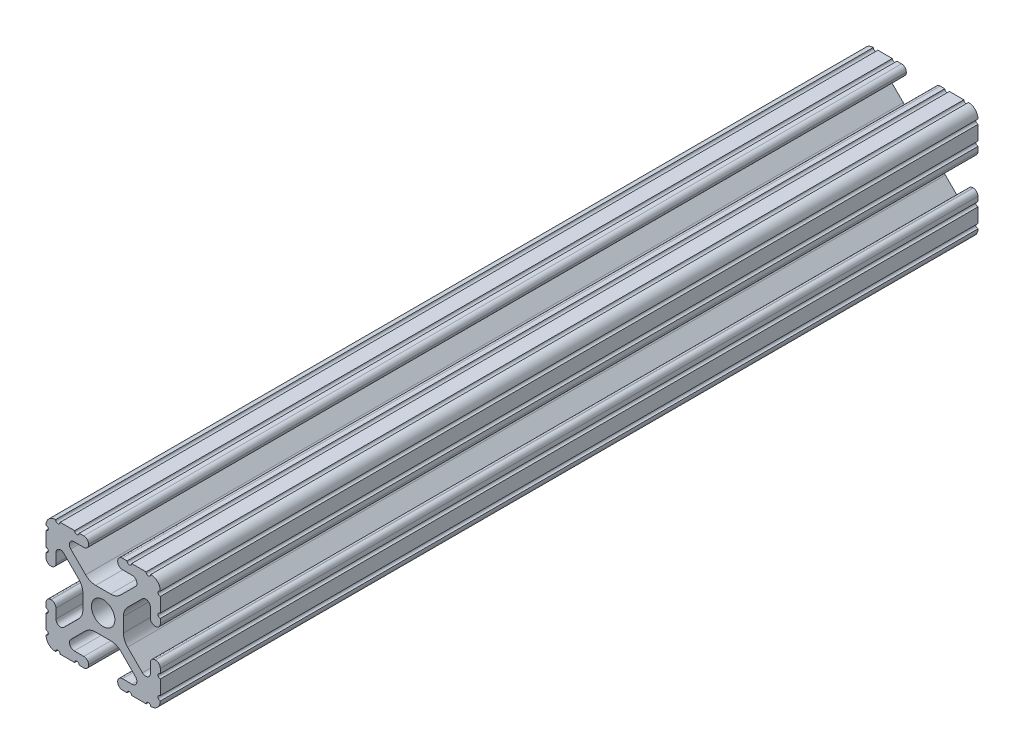
SolidWorks part; units mm, degrees
ref_plane "Front Plane" through (0, 0, 0) normal (0, 0, 1) x (1, 0, 0)
ref_plane "Top Plane" through (0, 0, 0) normal (0, 1, 0) x (1, 0, 0)
ref_plane "Right Plane" through (0, 0, 0) normal (1, 0, 0) x (0, 0, -1)
sketch "Sketch1" plane through (0, 0, 0) normal (0, 0, 1) x (1, 0, 0)
  line L88 (-7.1797, -8.6452) -> (-3.9523, -5.4237)
  line L89 (-1.7093, -4.4958) -> (1.7093, -4.4958)
  line L90 (3.9523, -5.4237) -> (7.1797, -8.6452)
  line L91 (6.4164, -10.4902) -> (4.2875, -10.4902)
  line L92 (3.2385, -11.5392) -> (3.2385, -11.651)
  line L93 (4.2875, -12.7) -> (5.3171, -12.7)
  line L94 (6.3331, -12.7) -> (9.5504, -12.7)
  line L95 (12.7, -9.5504) -> (12.7, -6.3331)
  line L96 (12.7, -5.3171) -> (12.7, -4.2875)
  line L97 (11.651, -3.2385) -> (11.5392, -3.2385)
  line L98 (10.4902, -4.2875) -> (10.4902, -6.4021)
  line L99 (8.7371, -7.1294) -> (5.441, -3.8408)
  line L100 (4.5085, -1.5932) -> (4.5085, 1.5932)
  line L101 (5.441, 3.8408) -> (8.7371, 7.1294)
  line L102 (10.4902, 6.4021) -> (10.4902, 4.2875)
  line L103 (11.5392, 3.2385) -> (11.651, 3.2385)
  line L104 (12.7, 4.2875) -> (12.7, 5.3171)
  line L105 (12.7, 6.3331) -> (12.7, 9.5504)
  line L106 (9.5504, 12.7) -> (6.3331, 12.7)
  line L107 (5.3171, 12.7) -> (4.2875, 12.7)
  line L108 (3.2385, 11.651) -> (3.2385, 11.5392)
  line L109 (4.2875, 10.4902) -> (6.4768, 10.4902)
  line L110 (7.207, 8.7244) -> (3.8983, 5.4232)
  line L111 (1.6558, 4.4958) -> (-1.6558, 4.4958)
  line L112 (-3.8983, 5.4232) -> (-7.207, 8.7244)
  line L113 (-6.4768, 10.4902) -> (-4.2875, 10.4902)
  line L114 (-3.2385, 11.5392) -> (-3.2385, 11.651)
  line L115 (-4.2875, 12.7) -> (-5.3171, 12.7)
  line L116 (-6.3331, 12.7) -> (-9.5504, 12.7)
  line L117 (-12.7, 9.5504) -> (-12.7, 6.3331)
  line L118 (-12.7, 5.3171) -> (-12.7, 4.2875)
  line L119 (-11.651, 3.2385) -> (-11.5392, 3.2385)
  line L120 (-10.4902, 4.2875) -> (-10.4902, 6.4021)
  line L121 (-8.7371, 7.1294) -> (-5.441, 3.8408)
  line L122 (-4.5085, 1.5932) -> (-4.5085, -1.5932)
  line L123 (-5.441, -3.8408) -> (-8.7371, -7.1294)
  line L124 (-10.4902, -6.4021) -> (-10.4902, -4.2875)
  line L125 (-11.5392, -3.2385) -> (-11.651, -3.2385)
  line L126 (-12.7, -4.2875) -> (-12.7, -5.3171)
  line L127 (-12.7, -6.3331) -> (-12.7, -9.5504)
  line L128 (-9.5504, -12.7) -> (-6.3331, -12.7)
  line L129 (-5.3171, -12.7) -> (-4.2875, -12.7)
  line L130 (-3.2385, -11.651) -> (-3.2385, -11.5392)
  line L131 (-4.2875, -10.4902) -> (-6.4164, -10.4902)
  circle A1 centre (0, 0) radius 2.6035
  arc A104 (-7.1797, -8.6452) -> (-6.4164, -10.4902) centre (-6.4164, -9.4098) ccw
  arc A105 (-1.7093, -4.4958) -> (-3.9523, -5.4237) centre (-1.7093, -7.6708) ccw
  arc A106 (3.9523, -5.4237) -> (1.7093, -4.4958) centre (1.7093, -7.6708) ccw
  arc A107 (6.4164, -10.4902) -> (7.1797, -8.6452) centre (6.4164, -9.4098) ccw
  arc A108 (4.2875, -10.4902) -> (3.2385, -11.5392) centre (4.2875, -11.5392) ccw
  arc A109 (3.2385, -11.651) -> (4.2875, -12.7) centre (4.2875, -11.651) ccw
  arc A110 (6.3331, -12.7) -> (5.3171, -12.7) centre (5.8251, -12.7) ccw
  arc A111 (10.5664, -12.6998) -> (9.5504, -12.7) centre (10.0584, -12.7) ccw
  arc A112 (10.5664, -12.6998) -> (12.6998, -10.5664) centre (10.5918, -10.5918) ccw
  arc A113 (12.7, -9.5504) -> (12.6998, -10.5664) centre (12.7, -10.0584) ccw
  arc A114 (12.7, -5.3171) -> (12.7, -6.3331) centre (12.7, -5.8251) ccw
  arc A115 (12.7, -4.2875) -> (11.651, -3.2385) centre (11.651, -4.2875) ccw
  arc A116 (11.5392, -3.2385) -> (10.4902, -4.2875) centre (11.5392, -4.2875) ccw
  arc A117 (8.7371, -7.1294) -> (10.4902, -6.4021) centre (9.4628, -6.4021) ccw
  arc A118 (4.5085, -1.5932) -> (5.441, -3.8408) centre (7.6835, -1.5932) ccw
  arc A119 (5.441, 3.8408) -> (4.5085, 1.5932) centre (7.6835, 1.5932) ccw
  arc A120 (10.4902, 6.4021) -> (8.7371, 7.1294) centre (9.4628, 6.4021) ccw
  arc A121 (10.4902, 4.2875) -> (11.5392, 3.2385) centre (11.5392, 4.2875) ccw
  arc A122 (11.651, 3.2385) -> (12.7, 4.2875) centre (11.651, 4.2875) ccw
  arc A123 (12.7, 6.3331) -> (12.7, 5.3171) centre (12.7, 5.8251) ccw
  arc A124 (12.6998, 10.5664) -> (12.7, 9.5504) centre (12.7, 10.0584) ccw
  arc A125 (12.6998, 10.5664) -> (10.5664, 12.6998) centre (10.5918, 10.5918) ccw
  arc A126 (9.5504, 12.7) -> (10.5664, 12.6998) centre (10.0584, 12.7) ccw
  arc A127 (5.3171, 12.7) -> (6.3331, 12.7) centre (5.8251, 12.7) ccw
  arc A128 (4.2875, 12.7) -> (3.2385, 11.651) centre (4.2875, 11.651) ccw
  arc A129 (3.2385, 11.5392) -> (4.2875, 10.4902) centre (4.2875, 11.5392) ccw
  arc A130 (7.207, 8.7244) -> (6.4768, 10.4902) centre (6.4768, 9.4563) ccw
  arc A131 (1.6558, 4.4958) -> (3.8983, 5.4232) centre (1.6558, 7.6708) ccw
  arc A132 (-3.8983, 5.4232) -> (-1.6558, 4.4958) centre (-1.6558, 7.6708) ccw
  arc A133 (-6.4768, 10.4902) -> (-7.207, 8.7244) centre (-6.4768, 9.4563) ccw
  arc A134 (-4.2875, 10.4902) -> (-3.2385, 11.5392) centre (-4.2875, 11.5392) ccw
  arc A135 (-3.2385, 11.651) -> (-4.2875, 12.7) centre (-4.2875, 11.651) ccw
  arc A136 (-6.3331, 12.7) -> (-5.3171, 12.7) centre (-5.8251, 12.7) ccw
  arc A137 (-10.5664, 12.6998) -> (-9.5504, 12.7) centre (-10.0584, 12.7) ccw
  arc A138 (-10.5664, 12.6998) -> (-12.6998, 10.5664) centre (-10.5918, 10.5918) ccw
  arc A139 (-12.7, 9.5504) -> (-12.6998, 10.5664) centre (-12.7, 10.0584) ccw
  arc A140 (-12.7, 5.3171) -> (-12.7, 6.3331) centre (-12.7, 5.8251) ccw
  arc A141 (-12.7, 4.2875) -> (-11.651, 3.2385) centre (-11.651, 4.2875) ccw
  arc A142 (-11.5392, 3.2385) -> (-10.4902, 4.2875) centre (-11.5392, 4.2875) ccw
  arc A143 (-8.7371, 7.1294) -> (-10.4902, 6.4021) centre (-9.4628, 6.4021) ccw
  arc A144 (-4.5085, 1.5932) -> (-5.441, 3.8408) centre (-7.6835, 1.5932) ccw
  arc A145 (-5.441, -3.8408) -> (-4.5085, -1.5932) centre (-7.6835, -1.5932) ccw
  arc A146 (-10.4902, -6.4021) -> (-8.7371, -7.1294) centre (-9.4628, -6.4021) ccw
  arc A147 (-10.4902, -4.2875) -> (-11.5392, -3.2385) centre (-11.5392, -4.2875) ccw
  arc A148 (-11.651, -3.2385) -> (-12.7, -4.2875) centre (-11.651, -4.2875) ccw
  arc A149 (-12.7, -6.3331) -> (-12.7, -5.3171) centre (-12.7, -5.8251) ccw
  arc A150 (-12.6998, -10.5664) -> (-12.7, -9.5504) centre (-12.7, -10.0584) ccw
  arc A151 (-12.6998, -10.5664) -> (-10.5664, -12.6998) centre (-10.5918, -10.5918) ccw
  arc A152 (-9.5504, -12.7) -> (-10.5664, -12.6998) centre (-10.0584, -12.7) ccw
  arc A153 (-5.3171, -12.7) -> (-6.3331, -12.7) centre (-5.8251, -12.7) ccw
  arc A154 (-4.2875, -12.7) -> (-3.2385, -11.651) centre (-4.2875, -11.651) ccw
  arc A155 (-3.2385, -11.5392) -> (-4.2875, -10.4902) centre (-4.2875, -11.5392) ccw
extrude "Boss-Extrude1" add sketch "Sketch1" along normal mid plane 181.75
